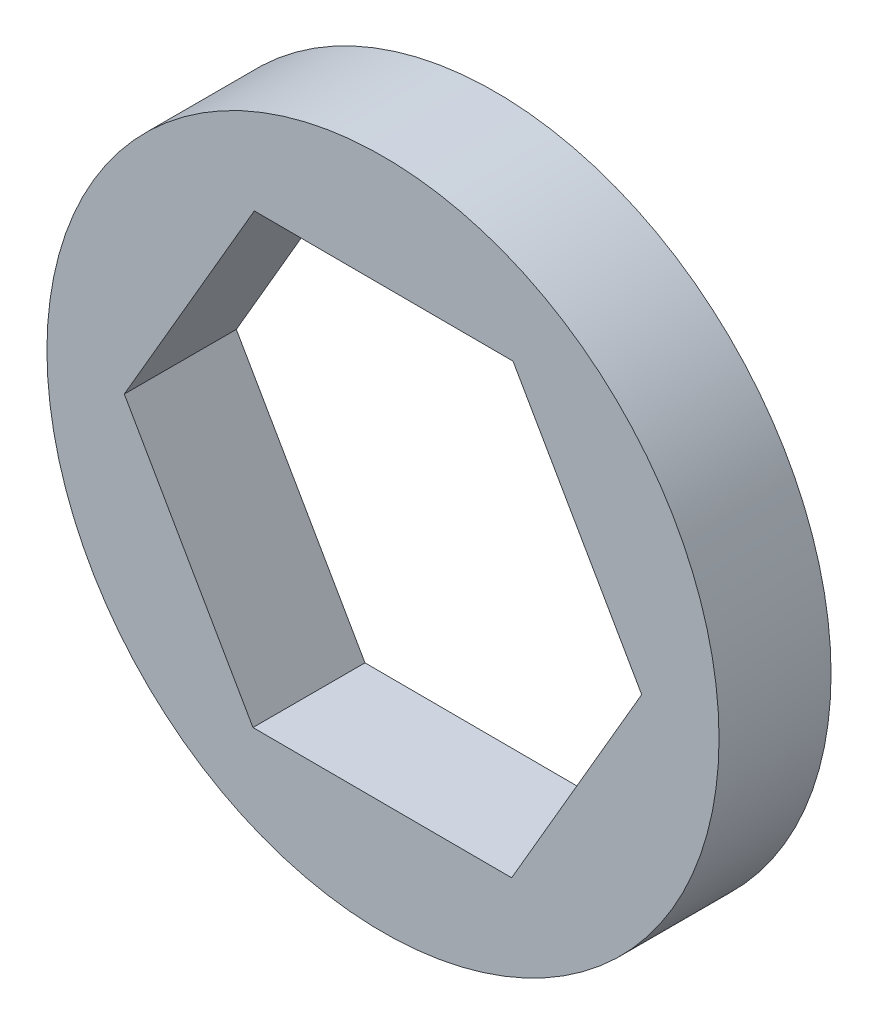
SolidWorks part; units mm, degrees
material "PET"
ref_plane "Front Plane" through (0, 0, 0) normal (0, 0, 1) x (1, 0, 0)
ref_plane "Top Plane" through (0, 0, 0) normal (0, 1, 0) x (1, 0, 0)
ref_plane "Right Plane" through (0, 0, 0) normal (1, 0, 0) x (0, 0, -1)
sketch "Sketch1" plane through (0, 0, 0) normal (0, 0, 1) x (1, 0, 0)
  line L1 (3.647, -6.361) -> (7.3323, -0.0221)
  line L2 (7.3323, -0.0221) -> (3.6853, 6.3389)
  line L3 (3.6853, 6.3389) -> (-3.647, 6.361)
  line L4 (-3.647, 6.361) -> (-7.3323, 0.0221)
  line L5 (-7.3323, 0.0221) -> (-3.6853, -6.3389)
  line L6 (-3.6853, -6.3389) -> (3.647, -6.361)
  circle A0 centre (0, 0) radius 9.525
  circle A1 centre (0, 0) radius 6.35 construction
  dimension "D1" = 19.05
  dimension "D2" = 12.7
extrude "Boss-Extrude1" add sketch "Sketch1" along normal blind 3.175
